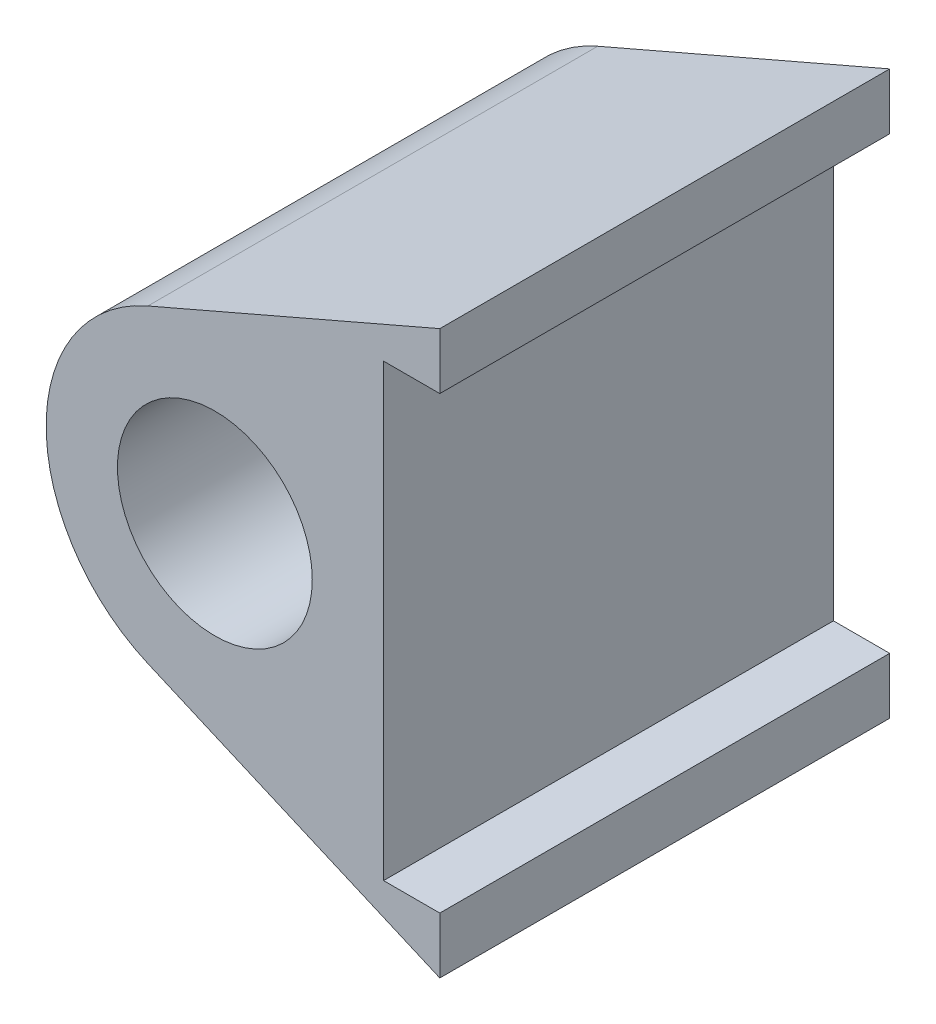
SolidWorks part; units mm, degrees
ref_plane "Front Plane" through (0, 0, 0) normal (0, 0, 1) x (1, 0, 0)
ref_plane "Top Plane" through (0, 0, 0) normal (0, 1, 0) x (1, 0, 0)
ref_plane "Right Plane" through (0, 0, 0) normal (1, 0, 0) x (0, 0, -1)
sketch "Sketch1" plane through (0, 0, 0) normal (0, 0, 1) x (1, 0, 0)
  line L0 (19.05, -25.4) -> (19.05, 25.4)
  line L1 (19.05, 25.4) -> (25.4, 25.4)
  line L2 (25.4, 25.4) -> (25.4, 31.75)
  line L3 (25.4, 31.75) -> (-7.5662, 17.483)
  line L4 (19.05, -25.4) -> (25.4, -25.4)
  line L5 (25.4, -25.4) -> (25.4, -31.75)
  line L6 (25.4, -31.75) -> (-7.5662, -17.483)
  circle A0 centre (0, 0) radius 10.9995
  arc A1 (-7.5662, 17.483) -> (-7.5662, -17.483) centre (0, 0) ccw
  point P7 (19.05, 0)
  dimension "D1" = 21.9989
  dimension "D2" = 38.1
  dimension "D3" = 50.8
  dimension "D4" = 6.35
  dimension "D5" = 6.35
  dimension "D6" = 19.05
extrude "Boss-Extrude1" add sketch "Sketch1" along normal blind 50.8
